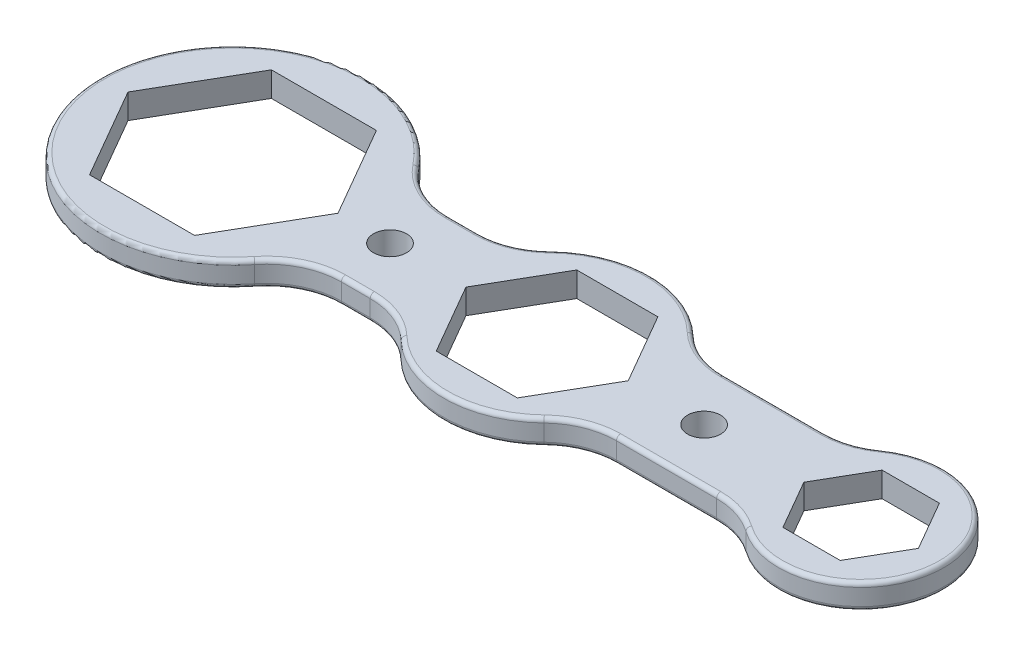
SolidWorks part; units mm, degrees
material "Alloy Steel"
ref_plane "Front Plane" through (0, 0, 0) normal (0, 0, 1) x (1, 0, 0)
ref_plane "Top Plane" through (0, 0, 0) normal (0, 1, 0) x (1, 0, 0)
ref_plane "Right Plane" through (0, 0, 0) normal (1, 0, 0) x (0, 0, -1)
sketch "Sketch1" plane through (0, 0, 0) normal (0, 1, 0) x (1, 0, 0)
  line L0 (-46.7596, 13) -> (-21.3542, 13)
  line L1 (0, 0) -> (-63.5135, 0) construction
  line L2 (-46.7596, -13) -> (-21.3542, -13)
  line L3 (21.3542, -13) -> (60.8013, -13)
  line L4 (21.3542, 13) -> (60.8013, 13)
  arc A0 (-21.3542, -13) -> (21.3542, -13) centre (0, 0) ccw
  arc A1 (60.8013, -13) -> (60.8013, 13) centre (76, 0) ccw
  arc A2 (-46.7596, 13) -> (-46.7596, -13) centre (-76, 0) ccw
  arc A3 (21.3542, 13) -> (-21.3542, 13) centre (0, 0) ccw
  dimension "D1" = 25
  dimension "D2" = 20
  dimension "D3" = 32
  dimension "D4" = 76
  dimension "D5" = 76
  dimension "D6" = 26
extrude "Boss-Extrude1" add sketch "Sketch1" along normal blind 6
sketch "Sketch2" plane through (0, 6, 0) normal (0, 1, 0) x (1, 0, 0)
  line L1 (19.6299, 0) -> (9.815, 17)
  line L2 (9.815, 17) -> (-9.815, 17)
  line L3 (-9.815, 17) -> (-19.6299, 0)
  line L4 (-19.6299, 0) -> (-9.815, -17)
  line L5 (-9.815, -17) -> (9.815, -17)
  line L6 (9.815, -17) -> (19.6299, 0)
  line L7 (89.8564, 0) -> (82.9282, 12)
  line L8 (82.9282, 12) -> (69.0718, 12)
  line L9 (69.0718, 12) -> (62.1436, 0)
  line L10 (62.1436, 0) -> (69.0718, -12)
  line L11 (69.0718, -12) -> (82.9282, -12)
  line L12 (82.9282, -12) -> (89.8564, 0)
  line L13 (-50.5966, 0) -> (-63.2983, 22)
  line L14 (-63.2983, 22) -> (-88.7017, 22)
  line L15 (-88.7017, 22) -> (-101.4034, 0)
  line L16 (-101.4034, 0) -> (-88.7017, -22)
  line L17 (-88.7017, -22) -> (-63.2983, -22)
  line L18 (-63.2983, -22) -> (-50.5966, 0)
  circle A0 centre (0, 0) radius 17 construction
  circle A1 centre (76, 0) radius 12 construction
  circle A2 centre (-76, 0) radius 22 construction
  dimension "D1" = 34
  dimension "D2" = 24
  dimension "D3" = 44
extrude "Cut-Extrude1" cut sketch "Sketch2" against normal through all
fillet "Fillet1" radius 18 8 edges at (60.8013, 3, 13) (60.8013, 3, -13) (21.3542, 3, 13) (21.3542, 3, -13) (-21.3542, 3, -13) (-21.3542, 3, 13) (-46.7596, 3, 13) (-46.7596, 3, -13)
sketch "Sketch3" plane through (0, 6, 0) normal (0, 1, 0) x (1, 0, 0)
  line L0 (0, 0) -> (0, 45.2572) construction
  circle A0 centre (-38, 0) radius 4
  circle A1 centre (38, 0) radius 4
  dimension "D1" = 8
  dimension "D2" = 38
extrude "Cut-Extrude2" cut sketch "Sketch3" against normal through all
fillet "Fillet3" radius 1 32 edges at (-44.6159, 0, -14.8) (-33.2846, 0, -13) (-23.0755, 0, -14.303) (0, 0, -25) (23.0755, 0, -14.303) (41.911, 0, -13) (59.4855, 0, -13.849) (96, 0, 0) (59.4855, 0, 13.849) (41.911, 0, 13) (23.0755, 0, 14.303) (0, 0, 25) (-23.0755, 0, 14.303) (-33.2846, 0, 13) (-44.6159, 0, 14.8) (-44.6159, 6, -14.8) (-33.2846, 6, -13) (-23.0755, 6, -14.303) (0, 6, -25) (23.0755, 6, -14.303) (41.911, 6, -13) (59.4855, 6, -13.849) (96, 6, 0) (59.4855, 6, 13.849) (41.911, 6, 13) (23.0755, 6, 14.303) (0, 6, 25) (-23.0755, 6, 14.303) (-33.2846, 6, 13) (-44.6159, 6, 14.8) (-108, 0, 0) (-108, 6, 0)
